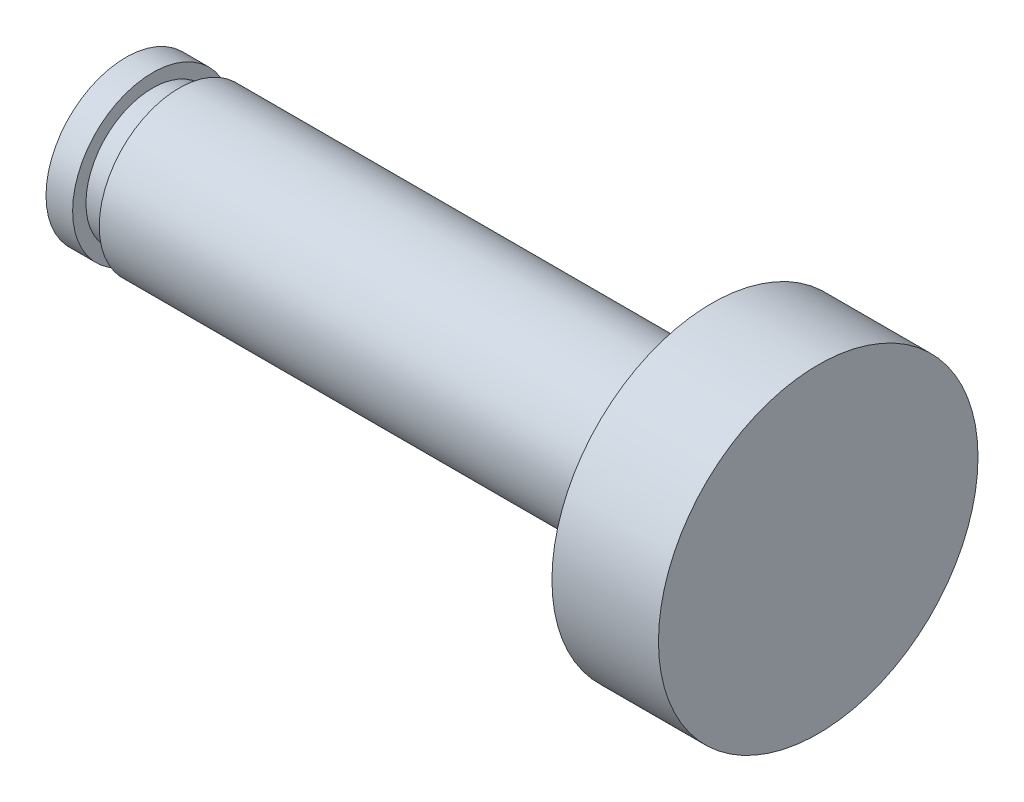
SolidWorks part; units mm, degrees
ref_plane "Front Plane" through (0, 0, 0) normal (0, 0, 1) x (1, 0, 0)
ref_plane "Top Plane" through (0, 0, 0) normal (0, 1, 0) x (1, 0, 0)
ref_plane "Right Plane" through (0, 0, 0) normal (1, 0, 0) x (0, 0, -1)
sketch "Sketch1" plane through (0, 0, 0) normal (0, 1, 0) x (1, 0, 0)
  line L0 (0, 0) -> (13, 0)
  line L1 (13, 0) -> (13, 3)
  line L2 (13, 3) -> (11, 3)
  line L3 (11, 3) -> (11, 1.5)
  line L4 (11, 1.5) -> (1, 1.5)
  line L5 (0, 1.5) -> (0, 0)
  line L6 (0, 0) -> (25859.2972, 0) construction
  line L7 (0.5, 1.5) -> (0, 1.5)
  line L9 (0.5, 1.5) -> (0.5, 1.25)
  line L10 (0.5, 1.25) -> (1, 1.25)
  line L11 (1, 1.5) -> (1, 1.25)
  dimension "D2" = 6
  dimension "D3" = 3
  dimension "D4" = 2
  dimension "D1" = 10
  dimension "D5" = 0.5
  dimension "D6" = 0.5
  dimension "D7" = 0.25
revolve "Revolve1" add sketch "Sketch1" angle 360 about L6
equation "\"D6@Sketch1\"=\"D5@Sketch1\""
equation "\"D7@Sketch1\"=\"D5@Sketch1\"/2"
